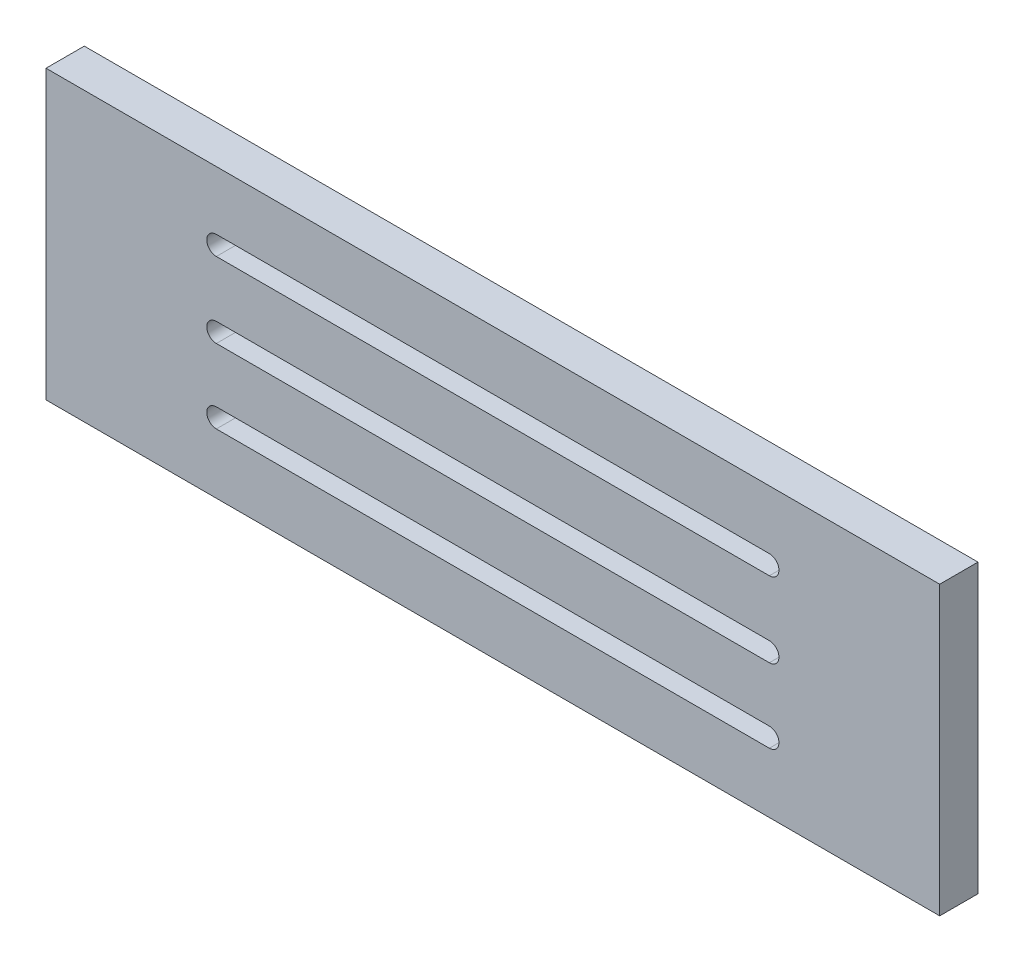
SolidWorks part; units mm, degrees
ref_plane "Front Plane" through (0, 0, 0) normal (0, 0, 1) x (1, 0, 0)
ref_plane "Top Plane" through (0, 0, 0) normal (0, 1, 0) x (1, 0, 0)
ref_plane "Right Plane" through (0, 0, 0) normal (1, 0, 0) x (0, 0, -1)
sketch "Sketch1" plane through (0, 0, 0) normal (0, 0, 1) x (1, 0, 0)
  line L0 (70, 45) -> (70, 0) construction
  line L1 (0, 0) -> (140, 0)
  line L2 (0, 0) -> (0, 45)
  line L3 (0, 45) -> (140, 45)
  line L4 (140, 0) -> (140, 45)
  line L5 (26.6832, 22.5) -> (113.3168, 22.5) construction
  line L6 (26.6832, 24) -> (113.3168, 24)
  line L7 (26.6832, 21) -> (113.3168, 21)
  line L8 (70, 34.3037) -> (113.3168, 34.3037) construction
  line L9 (113.3168, 34.3037) -> (26.6832, 34.3037) construction
  line L10 (26.6832, 34.3037) -> (113.3168, 34.3037) construction
  line L11 (26.6832, 35.8037) -> (113.3168, 35.8037)
  line L12 (26.6832, 32.8037) -> (113.3168, 32.8037)
  line L13 (70, 10.9053) -> (113.3168, 10.9053) construction
  line L14 (26.6832, 10.9053) -> (113.3168, 10.9053) construction
  line L15 (26.6832, 12.4053) -> (113.3168, 12.4053)
  line L16 (26.6832, 9.4053) -> (113.3168, 9.4053)
  arc A0 (26.6832, 24) -> (26.6832, 21) centre (26.6832, 22.5) ccw
  arc A1 (113.3168, 21) -> (113.3168, 24) centre (113.3168, 22.5) ccw
  arc A2 (26.6832, 35.8037) -> (26.6832, 32.8037) centre (26.6832, 34.3037) ccw
  arc A3 (113.3168, 32.8037) -> (113.3168, 35.8037) centre (113.3168, 34.3037) ccw
  arc A4 (26.6832, 12.4053) -> (26.6832, 9.4053) centre (26.6832, 10.9053) ccw
  arc A5 (113.3168, 9.4053) -> (113.3168, 12.4053) centre (113.3168, 10.9053) ccw
  point P9 (70, 22.5)
  point P18 (70, 34.3037)
  point P26 (70, 10.9053)
  dimension "D3" = 1.5
  dimension "D4" = 1.5
  dimension "D5" = 1.5
  dimension "D1" = 45
  dimension "D2" = 140
extrude "Boss-Extrude1" add sketch "Sketch1" along normal blind 6
